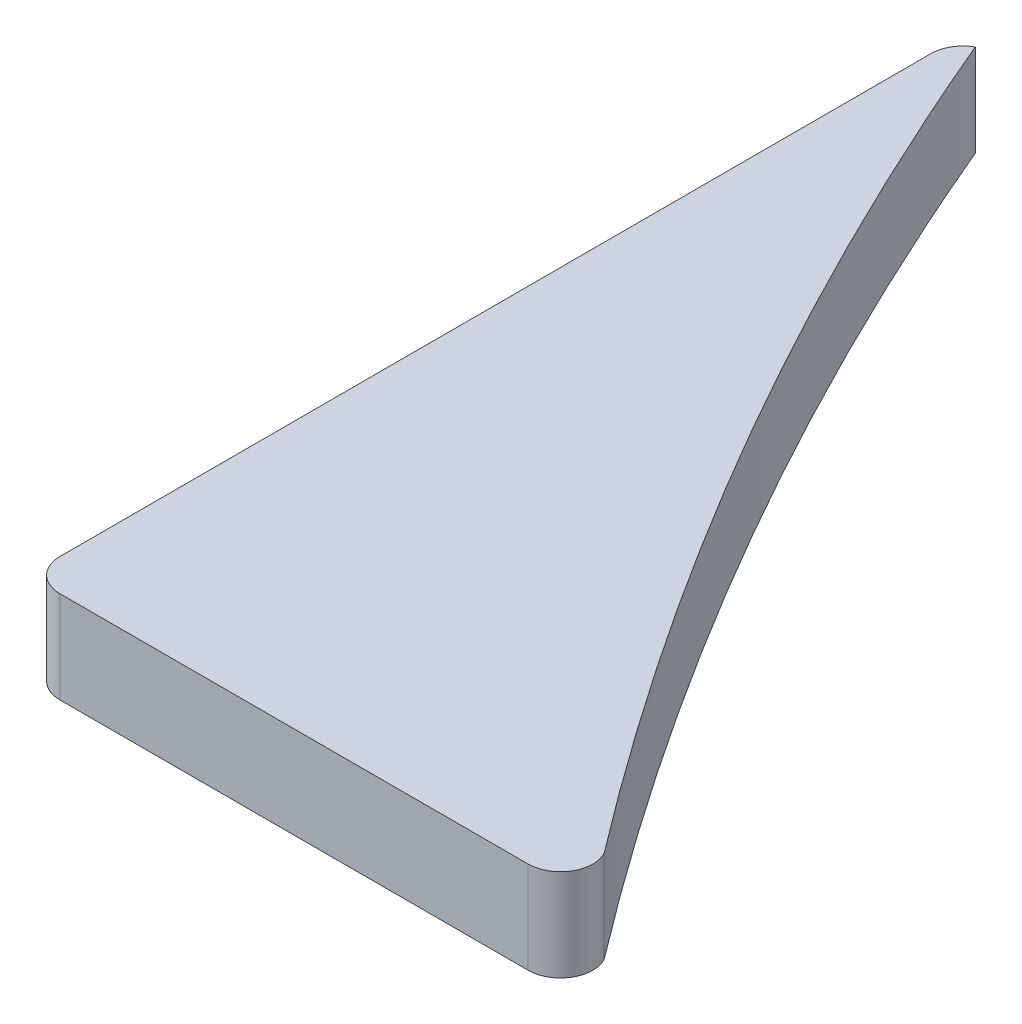
SolidWorks part; units mm, degrees
ref_plane "Front Plane" through (0, 0, 0) normal (0, 0, 1) x (1, 0, 0)
ref_plane "Top Plane" through (0, 0, 0) normal (0, 1, 0) x (1, 0, 0)
ref_plane "Right Plane" through (0, 0, 0) normal (1, 0, 0) x (0, 0, -1)
sketch "Sketch1" plane through (0, 0, 0) normal (0, 1, 0) x (1, 0, 0)
  line L0 (0, 2) -> (0, 55.936)
  line L2 (31, 0) -> (2, 0)
  arc A0 (0, 2) -> (2, 0) centre (2, 2) ccw
  arc A1 (32.7622, 2.9459) -> (31, 0) centre (31, 2) cw
  arc A2 (0, 55.936) -> (1.0162, 57.6773) centre (2, 55.936) cw
  spline S0 degree 2 poles (1.0162, 57.6773) (13.3909, 28.4129) (32.7622, 2.9459) knots 0 0 0 1 1 1
  point P6 (0, 0)
  point P12 (0, 0)
  point P13 (8.3431, 41.8855)
  point P14 (1.0162, 57.6773)
  dimension "D1" = 2
  dimension "D3" = 29
extrude "Boss-Extrude1" add sketch "Sketch1" along normal blind 5.7
